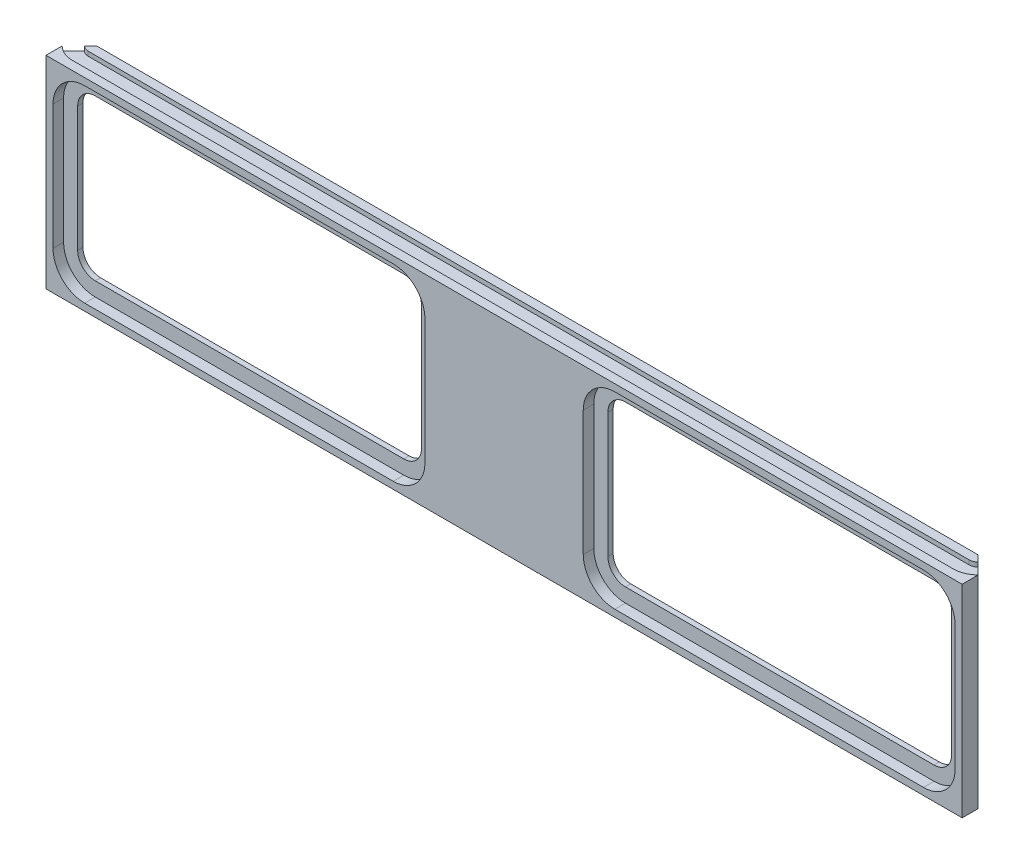
SolidWorks part; units mm, degrees
ref_plane "Front Plane" through (0, 0, 0) normal (0, 0, 1) x (1, 0, 0)
ref_plane "Top Plane" through (0, 0, 0) normal (0, 1, 0) x (1, 0, 0)
ref_plane "Right Plane" through (0, 0, 0) normal (1, 0, 0) x (0, 0, -1)
sketch "Sketch1" plane through (0, 0, 0) normal (0, 0, 1) x (1, 0, 0)
  line L1 (-260.35, 100) -> (260.35, 100)
  line L2 (-260.35, 100) -> (-260.35, -15)
  line L3 (-260.35, -15) -> (260.35, -15)
  line L4 (260.35, 100) -> (260.35, -15)
  dimension "D1" = 115
  dimension "D2" = 520.7
extrude "Boss-Extrude1" add sketch "Sketch1" along normal blind 9
sketch "Sketch2" plane through (0, 100, 0) normal (0, 1, 0) x (1, 0, 0)
  line L1 (-260.35, -9) -> (-260.35, 0) construction
  line L4 (-250.35, 10) -> (250.35, 10)
  line L5 (-260.35, 0) -> (-250.35, 10)
  line L6 (260.35, 0) -> (250.35, 10)
  line L7 (260.35, 0) -> (-260.35, 0) construction
  line L8 (260.35, 0) -> (-260.35, 0)
  line L9 (-260.35, 0) -> (-260.35, -9)
  line L10 (-260.35, -9) -> (260.35, -9)
  line L11 (260.35, -9) -> (260.35, 0)
  line L13 (-260.35, 0) -> (-260.35, -9)
  line L14 (-260.35, -9) -> (260.35, -9)
  line L15 (260.35, -9) -> (260.35, 0)
  dimension "D1" = 10
  dimension "D2" = 0
extrude "Boss-Extrude2" add sketch "Sketch2" against normal blind 10
sketch "Sketch3" plane through (0, 0, 9) normal (0, 0, 1) x (1, 0, 0)
  line L0 (260.35, 100) -> (-260.35, 100) construction
  line L1 (238.35, 88) -> (62.9918, 88)
  line L2 (248.35, 78) -> (248.35, 7)
  line L3 (238.35, -3) -> (62.9918, -3)
  line L4 (52.9918, 78) -> (52.9918, 7)
  line L5 (-260.35, -15) -> (260.35, -15) construction
  line L6 (260.35, -15) -> (260.35, 100) construction
  line L7 (44.9918, 43) -> (44.9918, 55.7) construction
  arc A0 (62.9918, -3) -> (52.9918, 7) centre (62.9918, 7) cw
  arc A1 (248.35, 7) -> (238.35, -3) centre (238.35, 7) cw
  arc A2 (238.35, 88) -> (248.35, 78) centre (238.35, 78) cw
  arc A3 (62.9918, 88) -> (52.9918, 78) centre (62.9918, 78) ccw
  dimension "D5" = 10
  dimension "D1" = 12
  dimension "D2" = 12
  dimension "D3" = 12
  dimension "D4" = 8
extrude "Cut-Extrude1" cut sketch "Sketch3" against normal up to surface (9 mm away) up to face at (0, 37.5, 0)
sketch "Sketch4" plane through (0, 0, 9) normal (0, 0, 1) x (1, 0, 0)
  line L8 (62.9918, -11) -> (238.35, -11)
  line L9 (44.9918, 78) -> (44.9918, 7)
  line L10 (238.35, 96) -> (62.9918, 96)
  line L11 (256.35, 7) -> (256.35, 78)
  line L12 (62.9918, -11) -> (238.35, -11)
  line L13 (44.9918, 78) -> (44.9918, 7)
  line L14 (238.35, 96) -> (62.9918, 96)
  line L15 (256.35, 7) -> (256.35, 78)
  arc A8 (44.9918, 7) -> (62.9918, -11) centre (62.9918, 7) ccw
  arc A9 (62.9918, 96) -> (44.9918, 78) centre (62.9918, 78) ccw
  arc A10 (256.35, 78) -> (238.35, 96) centre (238.35, 78) ccw
  arc A11 (238.35, -11) -> (256.35, 7) centre (238.35, 7) ccw
  arc A12 (44.9918, 7) -> (62.9918, -11) centre (62.9918, 7) ccw
  arc A13 (62.9918, 96) -> (44.9918, 78) centre (62.9918, 78) ccw
  arc A14 (256.35, 78) -> (238.35, 96) centre (238.35, 78) ccw
  arc A15 (238.35, -11) -> (256.35, 7) centre (238.35, 7) ccw
  dimension "D1" = 8
extrude "Cut-Extrude2" cut sketch "Sketch4" against normal blind 6
mirror "Mirror1" about plane through (0, 0, 0) normal (1, 0, 0) of "Cut-Extrude1", "Cut-Extrude2"
sketch "Sketch5" plane through (0, 100, 0) normal (0, 1, 0) x (1, 0, 0)
  line L0 (-250.35, 5) -> (250.35, 5)
  line L1 (-250.35, 10) -> (-260.35, 0) construction
  line L2 (260.35, 0) -> (250.35, 10) construction
  line L3 (250.35, 10) -> (-250.35, 10) construction
  line L4 (-250.35, -4) -> (250.35, -4)
  line L12 (253.8855, 6.4645) -> (260.2495, 0.1005)
  line L13 (-260.2495, 0.1005) -> (-253.8855, 6.4645)
  arc A0 (-250.35, 5) -> (-253.8855, 6.4645) centre (-250.35, 10) cw
  arc A1 (-250.35, -4) -> (-260.2495, 0.1005) centre (-250.35, 10) cw
  arc A2 (250.35, 5) -> (253.8855, 6.4645) centre (250.35, 10) ccw
  arc A3 (250.35, -4) -> (260.2495, 0.1005) centre (250.35, 10) ccw
  dimension "D1" = 5
  dimension "D2" = 9
extrude "Cut-Extrude3" cut sketch "Sketch5" against normal blind 2.5
